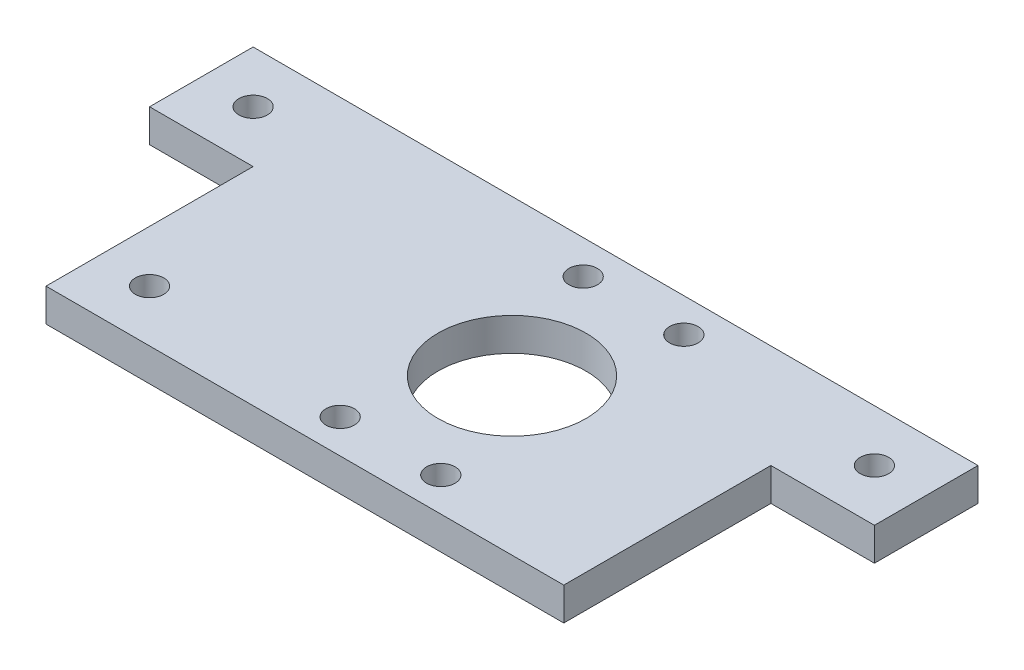
SolidWorks part; units mm, degrees
ref_plane "Front Plane" through (0, 0, 0) normal (0, 0, 1) x (1, 0, 0)
ref_plane "Top Plane" through (0, 0, 0) normal (0, 1, 0) x (1, 0, 0)
ref_plane "Right Plane" through (0, 0, 0) normal (1, 0, 0) x (0, 0, -1)
sketch "Sketch1" plane through (0, 0, 0) normal (0, 1, 0) x (1, 0, 0)
  line L1 (-58.7954, 3.7631) -> (81.2046, 3.7631)
  line L2 (-58.7954, 3.7631) -> (-58.7954, 63.7631)
  line L3 (-58.7954, 63.7631) -> (81.2046, 63.7631)
  line L4 (81.2046, 3.7631) -> (81.2046, 63.7631)
  dimension "D1" = 140
  dimension "D2" = 60
extrude "Boss-Extrude1" add sketch "Sketch1" along normal blind 6.35
sketch "Sketch3" plane through (0, 6.35, 0) normal (0, 1, 0) x (1, 0, 0)
  line L0 (81.2046, 33.7631) -> (-58.7954, 33.7631) construction
  line L1 (81.2046, 3.7631) -> (81.2046, 63.7631) construction
  line L2 (-58.7954, 63.7631) -> (-58.7954, 3.7631) construction
  line L3 (21.2046, 3.7631) -> (21.2046, 63.7631) construction
  line L4 (11.4846, 10.2965) -> (30.9246, 10.2965) construction
  line L5 (11.4846, 57.2297) -> (30.9246, 57.2297) construction
  line L9 (81.2046, 63.7631) -> (-58.7954, 63.7631) construction
  line L10 (-58.7954, 3.7631) -> (81.2046, 3.7631) construction
  circle A0 centre (21.2046, 33.7631) radius 14.295
  circle A4 centre (11.4846, 57.2297) radius 2.0193 construction
  circle A5 centre (30.9246, 57.2297) radius 2.0193 construction
  circle A13 centre (11.4846, 10.2965) radius 2.0193 construction
  circle A14 centre (30.9246, 10.2965) radius 2.0193 construction
  circle A15 centre (30.9246, 10.2965) radius 2.75
  circle A16 centre (11.4846, 10.2965) radius 2.75
  circle A17 centre (11.4846, 57.2297) radius 2.75
  circle A18 centre (30.9246, 57.2297) radius 2.75
  point P23 (-58.7954, 33.7631)
  point P24 (21.2046, 33.7631)
  dimension "D2" = 19.44
  dimension "D3" = 5.5
  dimension "D4" = 5.5
  dimension "D5" = 5.5
  dimension "D6" = 5.5
  dimension "D7" = 19.44
  dimension "D8" = 25.4
  dimension "D9" = 25.4
  dimension "D10" = 25.4
  dimension "D11" = 25.4
  dimension "D1" = 28.59
  dimension "D12" = 60
extrude "Cut-Extrude2" cut sketch "Sketch3" against normal through all contours A0
sketch "Sketch4" plane through (0, 6.35, 0) normal (0, 1, 0) x (1, 0, 0)
  line L0 (81.2046, 63.7631) -> (-58.7954, 63.7631) construction
  line L1 (81.2046, 3.7631) -> (61.2046, 3.7631)
  line L2 (81.2046, 3.7631) -> (81.2046, 43.7631)
  line L3 (81.2046, 43.7631) -> (61.2046, 43.7631)
  line L4 (61.2046, 3.7631) -> (61.2046, 43.7631)
  line L5 (-58.7954, 53.7631) -> (81.2046, 53.7631) construction
  line L6 (-58.7954, 3.7631) -> (-38.7954, 3.7631)
  line L7 (-58.7954, 3.7631) -> (-58.7954, 43.7631)
  line L8 (-58.7954, 43.7631) -> (-38.7954, 43.7631)
  line L9 (-38.7954, 3.7631) -> (-38.7954, 43.7631)
  line L10 (-58.7954, 63.7631) -> (-58.7954, 3.7631) construction
  line L11 (81.2046, 3.7631) -> (81.2046, 63.7631) construction
  line L12 (-58.7954, 3.7631) -> (81.2046, 3.7631) construction
  circle A0 centre (71.2046, 53.7631) radius 2.75
  circle A1 centre (-48.7954, 53.7631) radius 2.75
  circle A2 centre (-28.7954, 13.7631) radius 2.75
  dimension "D5" = 5.5
  dimension "D6" = 5.5
  dimension "D10" = 5.5
  dimension "D1" = 20
  dimension "D2" = 20
  dimension "D3" = 20
  dimension "D4" = 20
  dimension "D7" = 10
  dimension "D8" = 10
  dimension "D9" = 10
  dimension "D11" = 10
  dimension "D12" = 10
extrude "Cut-Extrude3" cut sketch "Sketch4" against normal up to next
